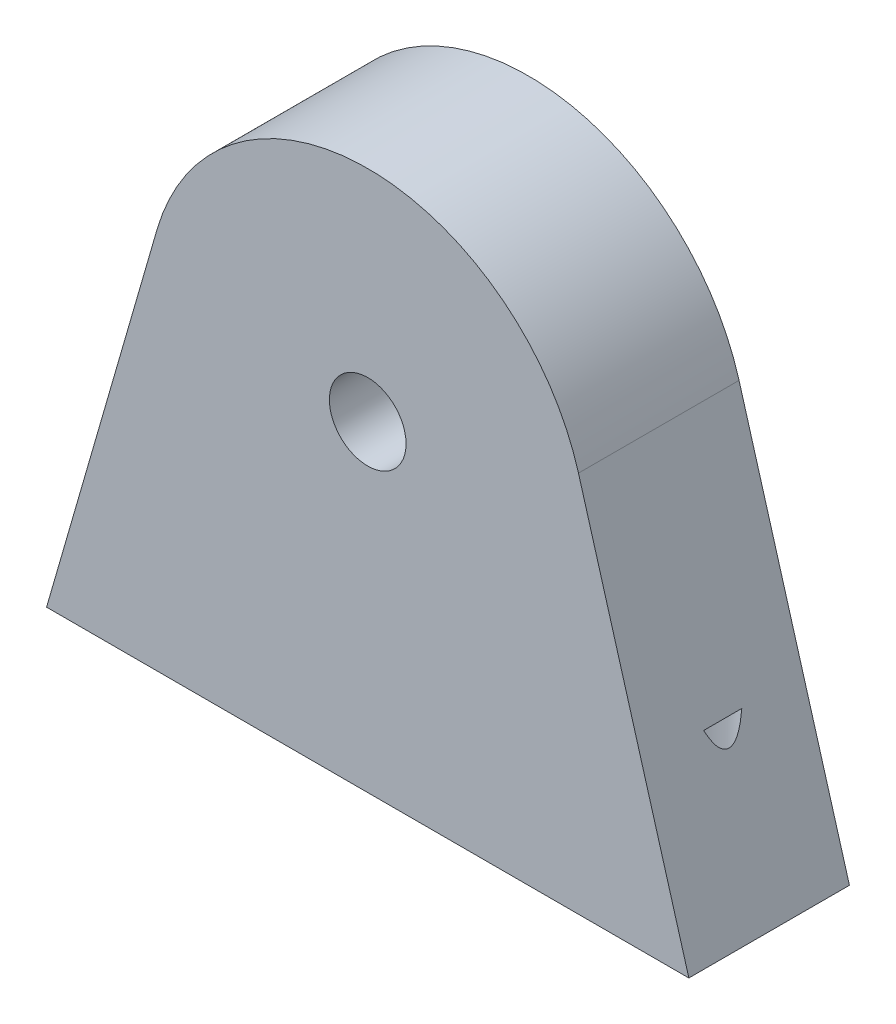
SolidWorks part; units mm, degrees
ref_plane "Front Plane" through (0, 0, 0) normal (0, 0, 1) x (1, 0, 0)
ref_plane "Top Plane" through (0, 0, 0) normal (0, 1, 0) x (1, 0, 0)
ref_plane "Right Plane" through (0, 0, 0) normal (1, 0, 0) x (0, 0, -1)
sketch "Sketch2" plane through (0, 0, 0) normal (0, 0, 1) x (1, 0, 0)
  line L0 (-20, 0) -> (20, 0)
  line L1 (-20, 0) -> (-13.1248, 23.7926)
  line L3 (13.1248, 23.7926) -> (20, 0)
  line L4 (0, -12.9804) -> (0, 65.5886) construction
  arc A0 (13.1248, 23.7926) -> (-13.1248, 23.7926) centre (0, 20) ccw
  circle A1 centre (0, 20) radius 2.3876
  point P4 (0, 0)
  dimension "D3" = 4.7752
  dimension "D4" = 20
  dimension "D1" = 40
  dimension "D2" = 26.2497
extrude "Boss-Extrude1" add sketch "Sketch2" along normal mid plane 10
sketch "Sketch3" plane through (0, 0, 0) normal (0, -1, 0) x (-1, 0, 0)
  line L0 (15.5, 0) -> (-15.5, 0) construction
  circle A0 centre (15.5, 0) radius 2
  circle A1 centre (-15.5, 0) radius 2
  point P8 (0, 0)
  dimension "D1" = 31
  dimension "D2" = 4
extrude "Cut-Extrude1" cut sketch "Sketch3" against normal blind 10
